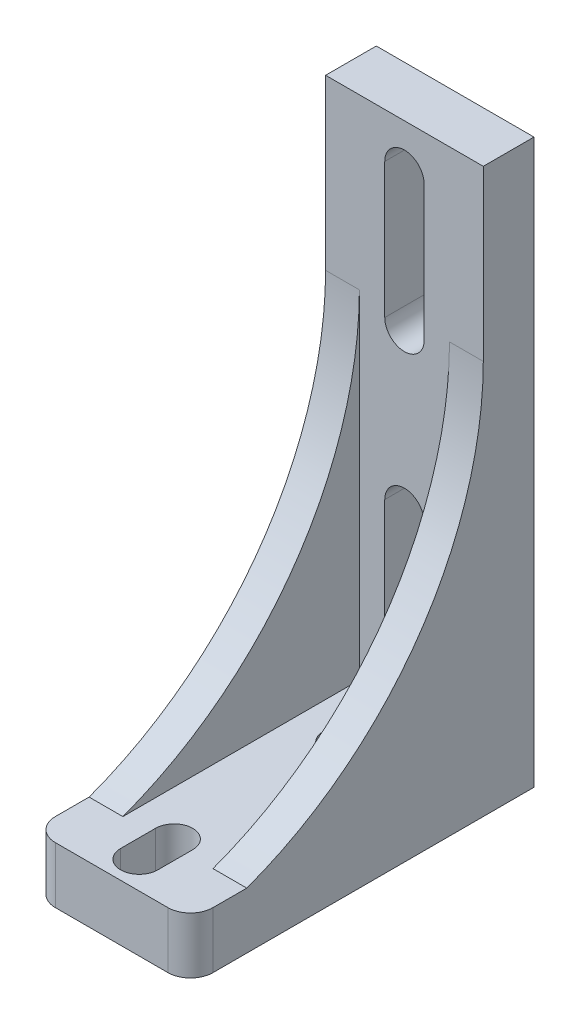
SolidWorks part; units mm, degrees
ref_plane "Alzado" through (0, 0, 0) normal (0, 0, 1) x (1, 0, 0)
ref_plane "Planta" through (0, 0, 0) normal (0, 1, 0) x (1, 0, 0)
ref_plane "Vista lateral" through (0, 0, 0) normal (1, 0, 0) x (0, 0, -1)
sketch "Croquis2" plane through (0, 0, 0) normal (0, 1, 0) x (1, 0, 0)
  line L0 (7, 31) -> (7, 0) construction
  line L1 (0, 0) -> (14, 0)
  line L2 (0, 0) -> (0, 31)
  line L3 (0, 31) -> (14, 31)
  line L4 (14, 0) -> (14, 31)
  circle A0 centre (7, 22) radius 1.55
  circle A1 centre (7, 4) radius 1.55
  dimension "D3" = 3.1
  dimension "D4" = 18
  dimension "D5" = 4
  dimension "D1" = 14
  dimension "D2" = 31
extrude "Saliente-Extruir1" add sketch "Croquis2" along normal blind 50
sketch "Croquis3" plane through (0, 0, 0) normal (-1, 0, 0) x (0, 0, 1)
  line L0 (-31, 50) -> (-31, 0) construction
  line L1 (0, 50) -> (-26, 50)
  line L2 (0, 50) -> (0, 5)
  line L3 (0, 5) -> (-26, 5)
  line L4 (-26, 50) -> (-26, 5)
  line L5 (-31, 0) -> (0, 0) construction
  dimension "D1" = 5
  dimension "D2" = 5
extrude "Cortar-Extruir1" cut sketch "Croquis3" against normal up to surface (14 mm away) up to face at (14, 25, -15.5)
sketch "Croquis4" plane through (0, 0, -31) normal (0, 0, -1) x (-1, 0, 0)
  line L0 (-7, 0) -> (-7, 50) construction
  line L1 (-14, 0) -> (0, 0) construction
  line L2 (-14, 50) -> (0, 50) construction
  line L3 (-14, 50) -> (-14, 0) construction
  line L5 (-7, 8) -> (-7, 20) construction
  line L6 (-8.75, 8) -> (-8.75, 20)
  line L7 (-5.25, 8) -> (-5.25, 20)
  line L8 (-7, 34) -> (-7, 46) construction
  line L9 (-8.75, 34) -> (-8.75, 46)
  line L10 (-5.25, 34) -> (-5.25, 46)
  arc A0 (-8.75, 8) -> (-5.25, 8) centre (-7, 8) ccw
  arc A1 (-5.25, 20) -> (-8.75, 20) centre (-7, 20) ccw
  arc A2 (-8.75, 34) -> (-5.25, 34) centre (-7, 34) ccw
  arc A3 (-5.25, 46) -> (-8.75, 46) centre (-7, 46) ccw
  point P8 (-7, 14)
  point P17 (-7, 40)
  dimension "D1" = 7
  dimension "D2" = 3.5
  dimension "D3" = 12
  dimension "D4" = 3.5
  dimension "D5" = 12
  dimension "D6" = 8
  dimension "D7" = 14
extrude "Cortar-Extruir2" cut sketch "Croquis4" against normal up to surface (5 mm away) up to face at (7, 27.5, -26)
sketch "Croquis6" plane through (0, 0, 0) normal (-1, 0, 0) x (0, 0, 1)
  line L3 (-26, 50) -> (-26, 5) construction
  line L9 (-26, 5) -> (0, 5) construction
  line L10 (-31, 50) -> (-26, 50) construction
  line L11 (0, 5) -> (0, 0) construction
  line L12 (-26, 5) -> (-26, 35)
  line L13 (-26, 5) -> (-5, 5)
  arc A1 (-26, 35) -> (-5, 5) centre (5.9975, 35.0482) ccw
  dimension "D1" = 15
  dimension "D2" = 5
extrude "Saliente-Extruir3" add sketch "Croquis6" against normal up to surface (14 mm away) up to face at (14, 18.3333, -19)
sketch "Croquis7" plane through (0, 50, 0) normal (0, 1, 0) x (1, 0, 0)
  line L0 (14, 0) -> (0, 0) construction
  line L2 (0, 26) -> (0, 0)
  line L3 (0, 0) -> (3, 0)
  line L4 (3, 26) -> (3, 0)
  line L7 (14, 26) -> (14, 0)
  line L8 (14, 0) -> (11, 0)
  line L9 (11, 26) -> (11, 0)
  line L10 (3, 26) -> (11, 26)
  line L11 (0, 26) -> (0, 31)
  line L12 (0, 31) -> (14, 31)
  line L13 (14, 26) -> (14, 31)
  dimension "D1" = 3
  dimension "D2" = 3
  dimension "D3" = 5
extrude "Cortar-Extruir5" cut sketch "Croquis7" against normal up to surface (45 mm away) flip side to cut up to face at (7, 5, -2.9083)
fillet "Redondeo1" radius 2 2 edges at (14, 2.5, 0) (0, 2.5, 0)
sketch "Croquis8" plane through (0, 50, 0) normal (0, 1, 0) x (1, 0, 0)
  line L11 (14, 26) -> (14, 31) construction
  line L12 (0, 31) -> (14, 31)
  line L13 (0, 31) -> (0, 30.5)
  line L14 (0, 30.5) -> (14, 30.5)
  line L15 (14, 31) -> (14, 30.5)
  dimension "D1" = 0.5
extrude "Cortar-Extruir6" cut sketch "Croquis8" against normal up to surface (50 mm away) up to face at (7, 0, -20.45)
sketch "Croquis9" plane through (0, 0, 0) normal (0, -1, 0) x (1, 0, 0)
  line L0 (7, -20.45) -> (7, -23.55) construction
  line L1 (8.65, -20.45) -> (8.65, -23.55)
  line L2 (5.35, -20.45) -> (5.35, -23.55)
  line L3 (7, -2.45) -> (7, -5.55) construction
  line L4 (8.65, -2.45) -> (8.65, -5.55)
  line L5 (5.35, -2.45) -> (5.35, -5.55)
  arc A0 (8.65, -20.45) -> (5.35, -20.45) centre (7, -20.45) ccw
  arc A1 (5.35, -23.55) -> (8.65, -23.55) centre (7, -23.55) ccw
  arc A2 (8.65, -2.45) -> (5.35, -2.45) centre (7, -2.45) ccw
  arc A3 (5.35, -5.55) -> (8.65, -5.55) centre (7, -5.55) ccw
  circle A4 centre (7, -4) radius 1.55 construction
  circle A5 centre (7, -22) radius 1.55 construction
  point P2 (7, -22)
  point P9 (7, -4)
  point P16 (7, -24.5276)
  point P17 (7, -5.55)
  point P20 (7, -23.55)
  dimension "D1" = 3.3
  dimension "D2" = 3.3
extrude "Cortar-Extruir7" cut sketch "Croquis9" against normal up to surface (5 mm away) up to face at (7, 5, -7.5172)
